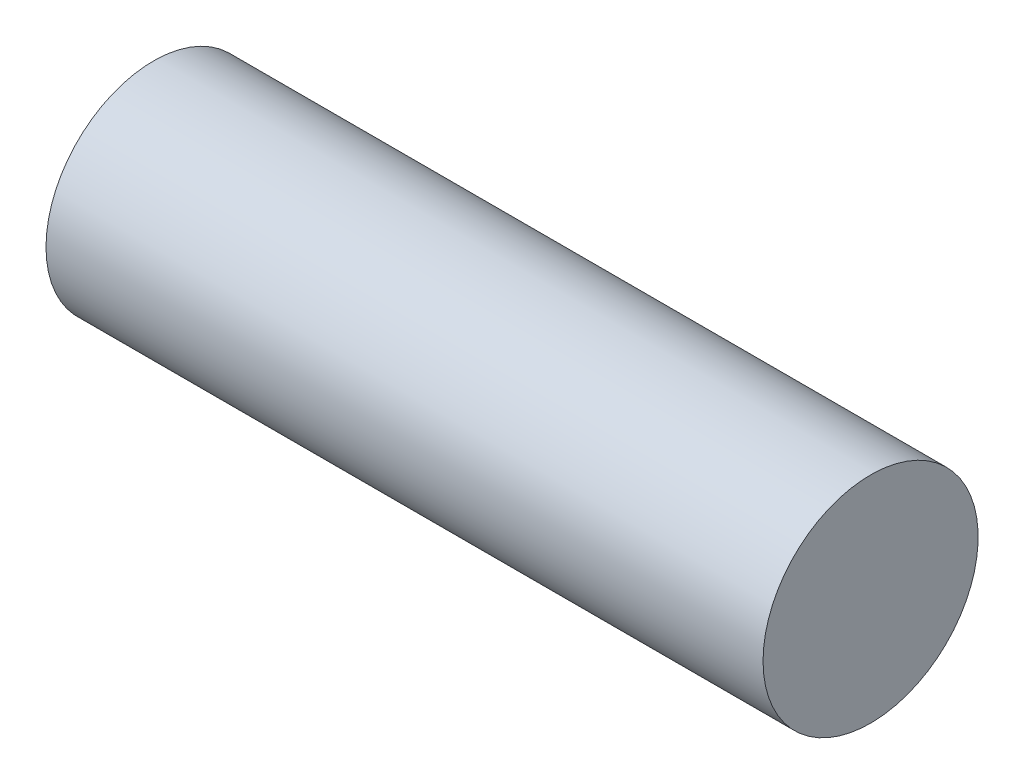
SolidWorks part; units mm, degrees
material "1023 al carbonio, lamiera (SS)"
ref_plane "Piano frontale" through (0, 0, 0) normal (0, 0, 1) x (1, 0, 0)
ref_plane "Piano superiore" through (0, 0, 0) normal (0, 1, 0) x (1, 0, 0)
ref_plane "Piano destro" through (0, 0, 0) normal (1, 0, 0) x (0, 0, -1)
sketch "Schizzo1" plane through (0, 0, 0) normal (0, 0, 1) x (1, 0, 0)
  line L1 (0, 0) -> (40, 0)
  line L2 (0, 0) -> (0, 6)
  line L3 (0, 6) -> (40, 6)
  line L4 (40, 0) -> (40, 6)
  dimension "D1" = 6
  dimension "D2" = 40
revolve "Rivoluzione1" add sketch "Schizzo1" angle 360 about L3
